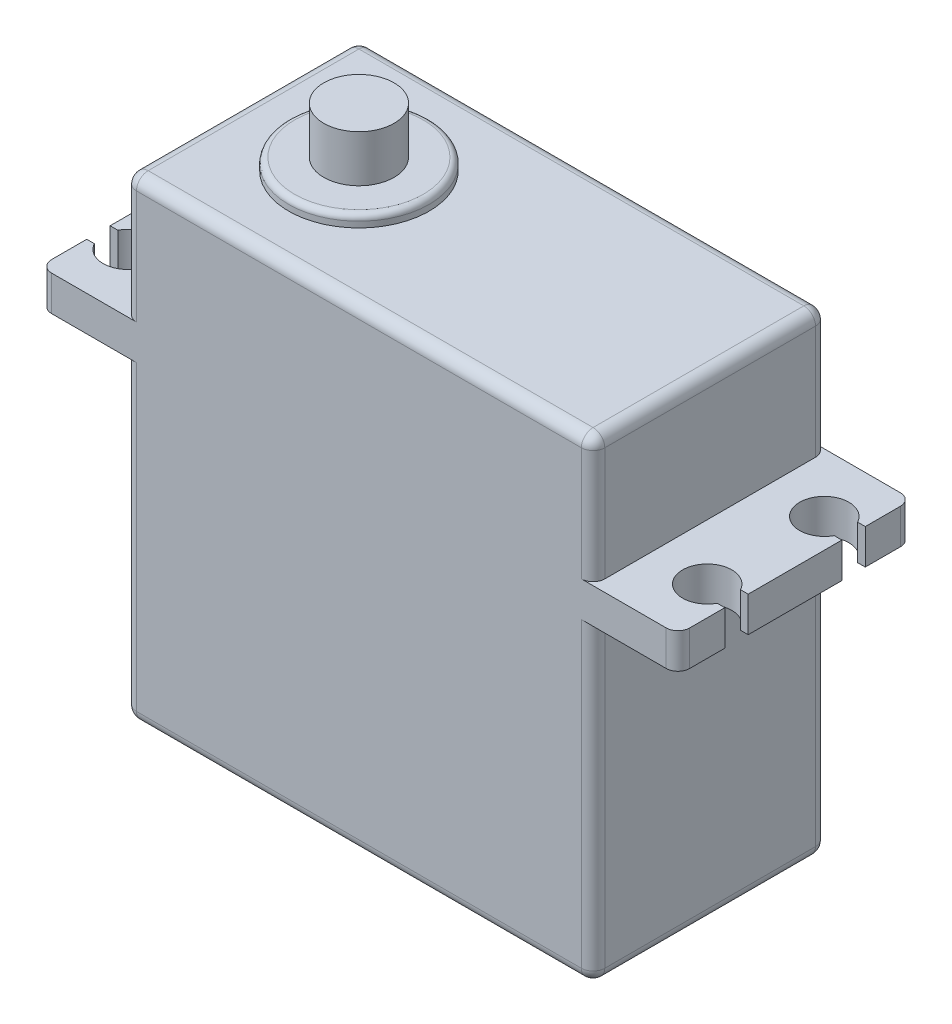
SolidWorks part; units mm, degrees
ref_plane "Front Plane" through (0, 0, 0) normal (0, 0, 1) x (1, 0, 0)
ref_plane "Top Plane" through (0, 0, 0) normal (0, 1, 0) x (1, 0, 0)
ref_plane "Right Plane" through (0, 0, 0) normal (1, 0, 0) x (0, 0, -1)
sketch "Sketch1" plane through (0, 0, 0) normal (0, 1, 0) x (1, 0, 0)
  line L1 (-20, -10) -> (20, -10)
  line L2 (-20, -10) -> (-20, 10)
  line L3 (-20, 10) -> (20, 10)
  line L4 (20, -10) -> (20, 10)
  line L5 (-20, -10) -> (20, 10) construction
  line L6 (-20, 10) -> (20, -10) construction
  point P0 (0, 0)
  dimension "D1" = 20
  dimension "D2" = 40
extrude "Boss-Extrude1" add sketch "Sketch1" along normal blind 40.5
ref_plane "Plane1" through (0, 26.8, 0) normal (0, 1, 0) x (1, 0, 0)
sketch "Sketch2" plane through (0, 26.8, 0) normal (0, 1, 0) x (1, 0, 0)
  line L0 (-28.9961, 0) -> (27.9005, 0) construction
  line L1 (20, 10) -> (27.25, 10)
  line L2 (20, -10) -> (27.25, -10)
  line L3 (27.25, 10) -> (27.25, -10)
  line L4 (0, 14.6441) -> (0, -15.6667) construction
  line L5 (20, 10) -> (20, -10)
  line L6 (27.25, 6) -> (27.25, 4)
  line L7 (26.5966, 4) -> (27.25, 4)
  line L8 (26.5966, 6) -> (27.25, 6)
  line L9 (26.5966, -4) -> (27.25, -4)
  line L10 (26.5966, -6) -> (27.25, -6)
  line L11 (27.25, -6) -> (27.25, -4)
  line L12 (-20, 10) -> (-20, -10)
  line L13 (-20, -10) -> (-27.25, -10)
  line L14 (-27.25, 10) -> (-27.25, -10)
  line L15 (-20, 10) -> (-27.25, 10)
  line L16 (-26.5966, -6) -> (-27.25, -6)
  line L17 (-27.25, -6) -> (-27.25, -4)
  line L18 (-26.5966, -4) -> (-27.25, -4)
  line L19 (-26.5966, 6) -> (-27.25, 6)
  line L20 (-26.5966, 4) -> (-27.25, 4)
  line L21 (-27.25, 6) -> (-27.25, 4)
  arc A0 (26.5966, 6) -> (26.5966, 4) centre (24.75, 5) ccw
  arc A3 (26.5966, -6) -> (26.5966, -4) centre (24.75, -5) cw
  arc A4 (-26.5966, -6) -> (-26.5966, -4) centre (-24.75, -5) ccw
  arc A5 (-26.5966, 6) -> (-26.5966, 4) centre (-24.75, 5) cw
  point P11 (24.75, 5)
  dimension "D5" = 4.2
  dimension "D1" = 10
  dimension "D2" = 27.25
  dimension "D3" = 24.75
  dimension "D4" = 5
  dimension "D6" = 20
  dimension "D8" = 1
extrude "Boss-Extrude2" add sketch "Sketch2" along normal blind 3 contours L19 A5 L20 L14 L18 A4 L16 L13 L12 L15 | L10 A3 L9 L3 L7 A0 L8 L1 L5 L2
fillet "Fillet1" radius 1 4 edges at (-27.25, 28.3, -10) (-27.25, 28.3, 10) (27.25, 28.3, -10) (27.25, 28.3, 10)
sketch "Sketch3" plane through (0, 40.5, 0) normal (0, 1, 0) x (1, 0, 0)
  line L0 (-20, 10) -> (-20, -10) construction
  circle A0 centre (-10, 0) radius 6
  point P0 (-10, 0)
  dimension "D2" = 12
  dimension "D1" = 10
extrude "Boss-Extrude3" add sketch "Sketch3" along normal blind 1
sketch "Sketch4" plane through (0, 41.5, 0) normal (0, 1, 0) x (1, 0, 0)
  circle A0 centre (-10, 0) radius 6 construction
  circle A1 centre (-10, 0) radius 3
  point P0 (-10, 0)
  dimension "D1" = 6
extrude "Boss-Extrude4" add sketch "Sketch4" along normal blind 4
fillet "Fillet2" radius 0.5 1 edges at (-10, 41.5, 6)
fillet "Fillet3" radius 1 16 edges at (20, 0, 0) (0, 0, -10) (0, 0, 10) (-20, 0, 0) (-20, 13.4, -10) (-20, 13.4, 10) (-20, 35.15, -10) (-20, 35.15, 10) (20, 13.4, -10) (20, 35.15, -10) (20, 13.4, 10) (20, 35.15, 10) (-20, 40.5, 0) (0, 40.5, -10) (20, 40.5, 0) (0, 40.5, 10)
